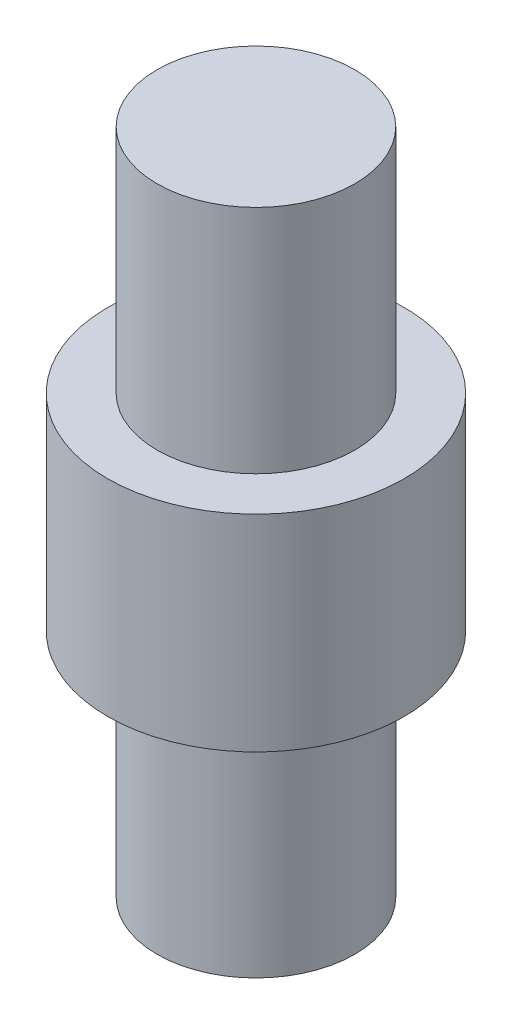
SolidWorks part; units mm, degrees
ref_plane "Front Plane" through (0, 0, 0) normal (0, 0, 1) x (1, 0, 0)
ref_plane "Top Plane" through (0, 0, 0) normal (0, 1, 0) x (1, 0, 0)
ref_plane "Right Plane" through (0, 0, 0) normal (1, 0, 0) x (0, 0, -1)
sketch "Sketch1" plane through (0, 0, 0) normal (0, 1, 0) x (1, 0, 0)
  circle A0 centre (0, 0) radius 2.286
  dimension "D1" = 4.572
extrude "Boss-Extrude1" add sketch "Sketch1" along normal mid plane 3.175
sketch "Sketch2" plane through (0, -1.5875, 0) normal (0, -1, 0) x (-1, 0, 0)
  circle A0 centre (0, 0) radius 1.524
  dimension "D1" = 3.048
extrude "Boss-Extrude2" add sketch "Sketch2" along normal blind 3.556
mirror "Mirror1" about plane through (0, 0, 0) normal (0, 1, 0) of "Boss-Extrude2"
